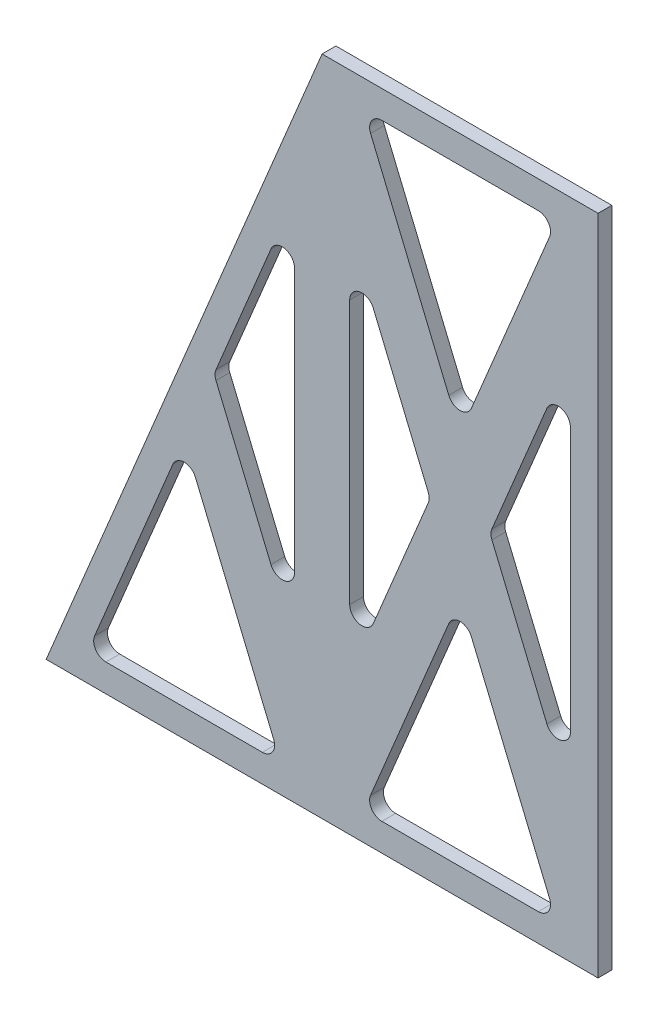
SolidWorks part; units mm, degrees
ref_plane "Front Plane" through (0, 0, 0) normal (0, 0, 1) x (1, 0, 0)
ref_plane "Top Plane" through (0, 0, 0) normal (0, 1, 0) x (1, 0, 0)
ref_plane "Right Plane" through (0, 0, 0) normal (1, 0, 0) x (0, 0, -1)
sketch "Sketch2" plane through (0, 0, 0) normal (0, 0, 1) x (1, 0, 0)
  line L0 (-31.75, -76.2) -> (-95.25, -76.2)
  line L1 (-31.75, -76.2) -> (31.75, -76.2)
  line L2 (-31.75, -76.2) -> (-31.75, 76.2) construction
  line L3 (-31.75, 76.2) -> (31.75, 76.2)
  line L4 (31.75, -76.2) -> (31.75, 76.2)
  line L5 (-31.75, -76.2) -> (31.75, 76.2) construction
  line L6 (-31.75, 76.2) -> (31.75, -76.2) construction
  line L7 (-95.25, -76.2) -> (-31.75, 76.2)
  point P0 (0, 0)
  dimension "D1" = 63.5
  dimension "D2" = 152.4
extrude "Boss-Extrude1" add sketch "Sketch2" along normal mid plane 3.175
sketch "Sketch3" plane through (0, 0, 1.5875) normal (0, 0, 1) x (1, 0, 0)
  line L0 (-31.75, 76.2) -> (0, 0) construction
  line L1 (31.75, -76.2) -> (-31.75, -76.2) construction
  line L2 (31.75, -76.2) -> (31.75, 76.2) construction
  line L3 (31.75, 76.2) -> (-31.75, 76.2) construction
  line L4 (-31.75, -76.2) -> (-31.75, 76.2) construction
  line L5 (31.75, -76.2) -> (-31.75, 76.2) construction
  line L6 (31.75, 76.2) -> (-31.75, -76.2) construction
  line L7 (0, 0) -> (31.75, 76.2) construction
  line L8 (31.75, 76.2) -> (-31.75, 76.2) construction
  line L9 (17.996, 69.85) -> (-17.996, 69.85)
  line L10 (-20.5985, 65.9463) -> (-2.6024, 22.7559)
  line L11 (2.6024, 22.7559) -> (20.5985, 65.9463)
  line L12 (0, 0) -> (-31.75, -76.2) construction
  line L13 (-31.75, -76.2) -> (31.75, -76.2) construction
  line L14 (31.75, -76.2) -> (0, 0) construction
  line L15 (20.5985, -65.9463) -> (2.6024, -22.7559)
  line L16 (-2.6024, -22.7559) -> (-20.5985, -65.9463)
  line L17 (-17.996, -69.85) -> (17.996, -69.85)
  line L18 (-31.75, 76.2) -> (-31.75, -76.2) construction
  line L19 (-31.75, -76.2) -> (0, 0) construction
  line L20 (0, 0) -> (-31.75, 76.2) construction
  line L21 (-7.331, 1.0844) -> (-19.9782, 31.4378)
  line L22 (-25.4, 30.3534) -> (-25.4, -30.3534)
  line L23 (-19.9782, -31.4378) -> (-7.331, -1.0844)
  line L24 (31.75, 76.2) -> (0, 0) construction
  line L25 (0, 0) -> (31.75, -76.2) construction
  line L26 (31.75, -76.2) -> (31.75, 76.2) construction
  line L27 (25.4, -30.3534) -> (25.4, 30.3534)
  line L28 (19.9782, 31.4378) -> (7.331, 1.0844)
  line L29 (7.331, -1.0844) -> (19.9782, -31.4378)
  line L30 (-22.225, -69.85) -> (22.225, -69.85) construction
  line L31 (22.225, -69.85) -> (0, -16.51) construction
  line L32 (0, -16.51) -> (-22.225, -69.85) construction
  line L33 (0, 16.51) -> (22.225, 69.85) construction
  line L34 (22.225, 69.85) -> (-22.225, 69.85) construction
  line L35 (-22.225, 69.85) -> (0, 16.51) construction
  line L36 (25.4, -44.45) -> (25.4, 44.45) construction
  line L37 (6.8792, 0) -> (25.4, -44.45) construction
  line L38 (25.4, 44.45) -> (6.8792, 0) construction
  line L39 (-25.4, -44.45) -> (-6.8792, 0) construction
  line L40 (-6.8792, 0) -> (-25.4, 44.45) construction
  line L41 (-25.4, 44.45) -> (-25.4, -44.45) construction
  line L42 (-95.25, -76.2) -> (-31.75, 76.2) construction
  line L43 (-31.75, 76.2) -> (-31.75, -76.2) construction
  line L44 (-95.25, -76.2) -> (-31.75, -76.2) construction
  line L46 (-63.5, 0) -> (-31.75, 76.2) construction
  line L47 (-31.75, 76.2) -> (-31.75, 0) construction
  line L51 (-43.5218, -31.4378) -> (-56.169, -1.0844)
  line L52 (-38.1, 30.3534) -> (-38.1, -30.3534)
  line L53 (-56.169, 1.0844) -> (-43.5218, 31.4378)
  line L54 (-60.8976, -22.7559) -> (-42.9015, -65.9463)
  line L55 (-84.0985, -65.9463) -> (-66.1024, -22.7559)
  line L56 (-45.504, -69.85) -> (-81.496, -69.85)
  arc A0 (17.996, -69.85) -> (20.5985, -65.9463) centre (17.996, -67.0307) ccw
  arc A1 (-17.996, -69.85) -> (-20.5985, -65.9463) centre (-17.996, -67.0307) cw
  arc A2 (-2.6024, -22.7559) -> (2.6024, -22.7559) centre (0, -23.8402) cw
  arc A3 (20.5985, 65.9463) -> (17.996, 69.85) centre (17.996, 67.0307) ccw
  arc A4 (2.6024, 22.7559) -> (-2.6024, 22.7559) centre (0, 23.8402) cw
  arc A5 (-20.5985, 65.9463) -> (-17.996, 69.85) centre (-17.996, 67.0307) cw
  arc A6 (25.4, -30.3534) -> (19.9782, -31.4378) centre (22.5807, -30.3534) cw
  arc A7 (19.9782, 31.4378) -> (25.4, 30.3534) centre (22.5807, 30.3534) cw
  arc A8 (7.331, -1.0844) -> (7.331, 1.0844) centre (9.9334, 0) cw
  arc A9 (-7.331, -1.0844) -> (-7.331, 1.0844) centre (-9.9334, 0) ccw
  arc A10 (-19.9782, -31.4378) -> (-25.4, -30.3534) centre (-22.5807, -30.3534) cw
  arc A11 (-25.4, 30.3534) -> (-19.9782, 31.4378) centre (-22.5807, 30.3534) cw
  arc A12 (-49.746, 6.35) -> (-52.3485, 10.2537) centre (-49.746, 9.1693) cw
  arc A15 (-38.1, 30.3534) -> (-43.5218, 31.4378) centre (-40.9193, 30.3534) ccw
  arc A16 (-43.5218, -31.4378) -> (-38.1, -30.3534) centre (-40.9193, -30.3534) ccw
  arc A17 (-56.169, -1.0844) -> (-56.169, 1.0844) centre (-53.5666, 0) cw
  arc A18 (-45.504, -69.85) -> (-42.9015, -65.9463) centre (-45.504, -67.0307) ccw
  arc A19 (-81.496, -69.85) -> (-84.0985, -65.9463) centre (-81.496, -67.0307) cw
  arc A20 (-60.8976, -22.7559) -> (-66.1024, -22.7559) centre (-63.5, -23.8402) ccw
  point P0 (0, 0)
  point P60 (-31.4646, 0)
  point P61 (0, 0)
  dimension "D5" = 2.8193
  dimension "D1" = 6.35
  dimension "D2" = 6.35
  dimension "D3" = 6.35
  dimension "D4" = 6.35
extrude "Cut-Extrude1" cut sketch "Sketch3" against normal blind 5.08 contours L54 A20 L55 A19 L56 A18 | A11 L22 A10 L23 A9 L21 | A5 L10 A4 L11 A3 L9 | A2 L16 A1 L17 A0 L15 | L52 A16 L51 A17 L53 A15 | L27 A7 L28 A8 L29 A6
